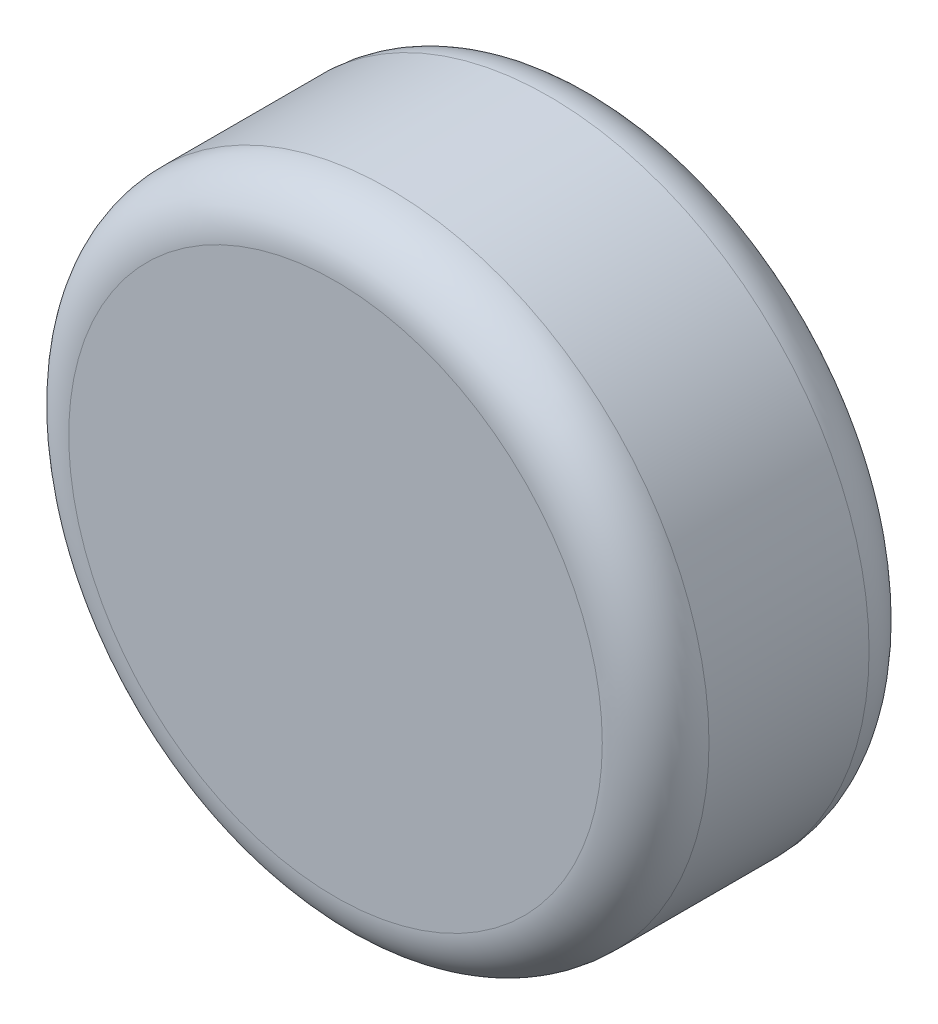
SolidWorks part; units mm, degrees
ref_plane "Front Plane" through (0, 0, 0) normal (0, 0, 1) x (1, 0, 0)
ref_plane "Top Plane" through (0, 0, 0) normal (0, 1, 0) x (1, 0, 0)
ref_plane "Right Plane" through (0, 0, 0) normal (1, 0, 0) x (0, 0, -1)
sketch "Sketch1" plane through (0, 0, 0) normal (0, 0, 1) x (1, 0, 0)
  circle A0 centre (0, 0) radius 30
extrude "Boss-Extrude1" add sketch "Sketch1" along normal blind 25
fillet "Fillet1" radius 5 2 edges at (30, 0, 0) (30, 0, 25)
